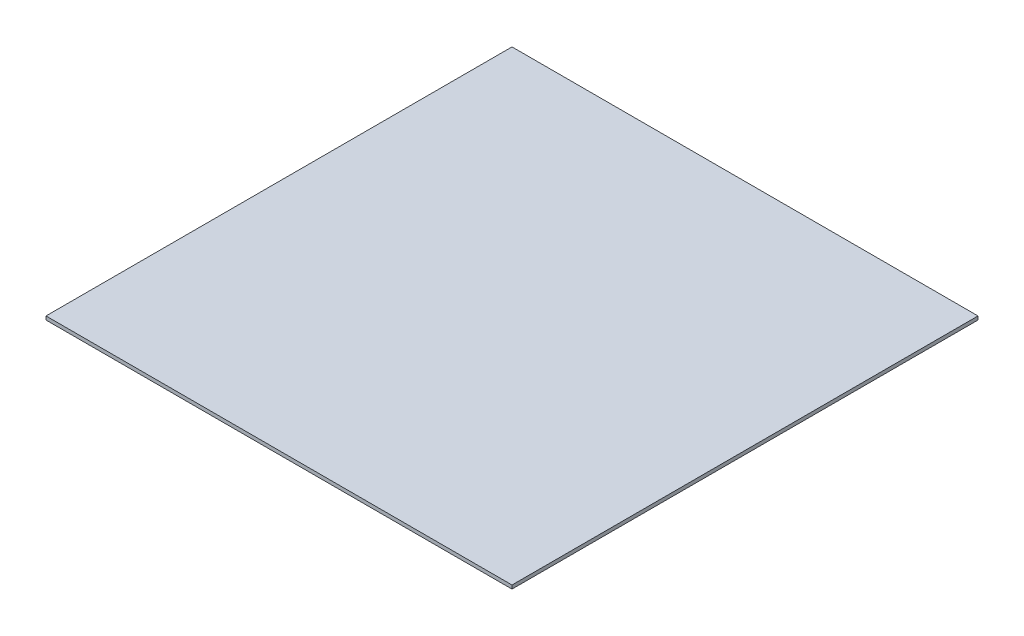
SolidWorks part; units mm, degrees
ref_plane "Front Plane" through (0, 0, 0) normal (0, 0, 1) x (1, 0, 0)
ref_plane "Top Plane" through (0, 0, 0) normal (0, 1, 0) x (1, 0, 0)
ref_plane "Right Plane" through (0, 0, 0) normal (1, 0, 0) x (0, 0, -1)
sketch "Sketch1" plane through (0, 0, 0) normal (0, 1, 0) x (1, 0, 0)
  line L1 (-47.0317, 81.8994) -> (82.9683, 81.8994)
  line L2 (-47.0317, 81.8994) -> (-47.0317, -48.1006)
  line L3 (-47.0317, -48.1006) -> (82.9683, -48.1006)
  line L4 (82.9683, 81.8994) -> (82.9683, -48.1006)
  dimension "D1" = 130
  dimension "D2" = 130
extrude "Boss-Extrude1" add sketch "Sketch1" along normal blind 1
